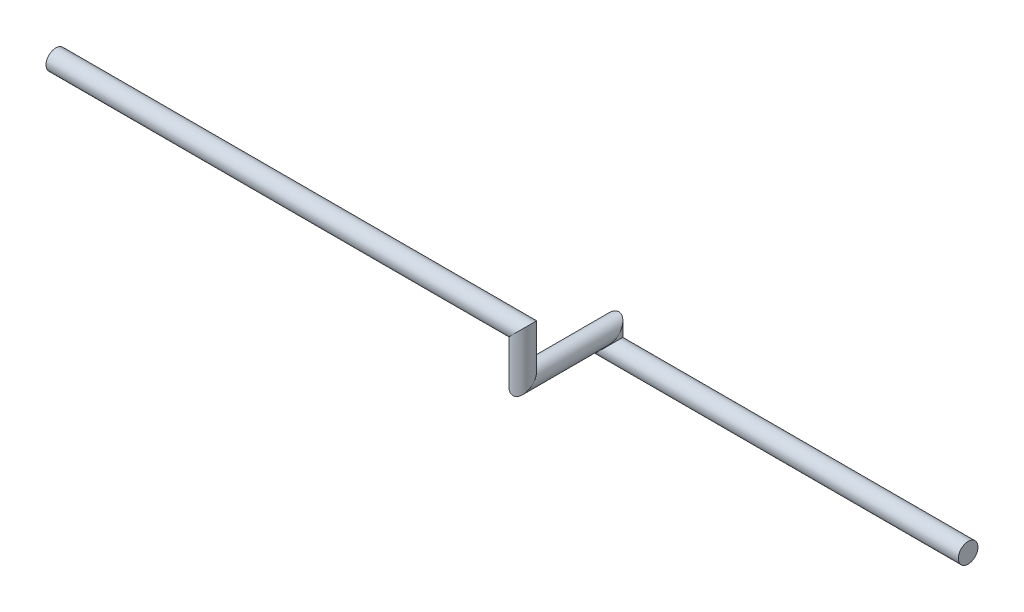
SolidWorks part; units mm, degrees
ref_plane "Alzado" through (0, 0, 0) normal (0, 0, 1) x (1, 0, 0)
ref_plane "Planta" through (0, 0, 0) normal (0, 1, 0) x (1, 0, 0)
ref_plane "Vista lateral" through (0, 0, 0) normal (1, 0, 0) x (0, 0, -1)
sketch3d "Croquis3D1"
  line L0 (0, 0, 0) -> (-500, 0, 0)
  line L1 (-500, 0, 0) -> (-500, 20, 0)
  line L2 (-500, 20, 0) -> (-500, 20, 120)
  line L3 (-500, 20, 120) -> (-500, 80, 120)
  line L4 (-500, 80, 120) -> (-1150, 80, 120)
  dimension "D1" = 500
  dimension "D2" = 20
  dimension "D3" = 120
  dimension "D4" = 60
  dimension "D5" = 650
sketch "Croquis1" plane through (0, 0, 0) normal (1, 0, 0) x (0, 0, -1)
  circle A0 centre (0, 0) radius 13.7
  dimension "D1" = 27.4
sweep "Barrer1" add profiles "Croquis1" path "Croquis3D1"
